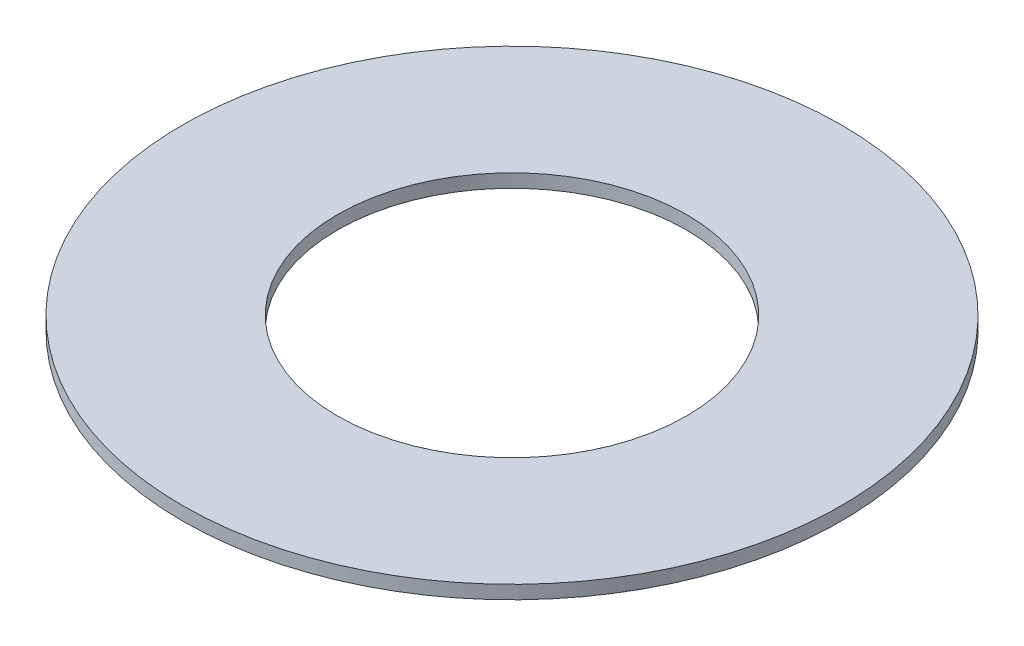
SolidWorks part; units mm, degrees
ref_plane "Front Plane" through (0, 0, 0) normal (0, 0, 1) x (1, 0, 0)
ref_plane "Top Plane" through (0, 0, 0) normal (0, 1, 0) x (1, 0, 0)
ref_plane "Right Plane" through (0, 0, 0) normal (1, 0, 0) x (0, 0, -1)
sketch "Sketch1" plane through (0, 0, 0) normal (0, 1, 0) x (1, 0, 0)
  circle A0 centre (0, 0) radius 2.6
  circle A1 centre (0, 0) radius 4.91
  dimension "D1" = 5.2
  dimension "D2" = 9.82
extrude "Boss-Extrude1" add sketch "Sketch1" along normal blind 0.2
